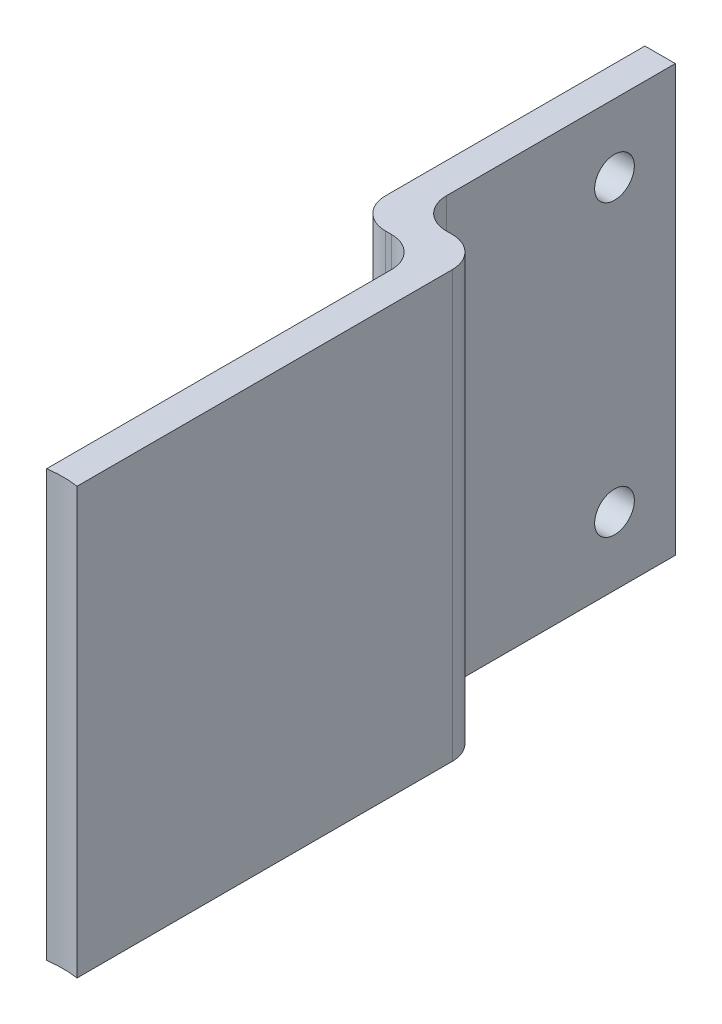
SolidWorks part; units mm, degrees
ref_plane "Front Plane" through (0, 0, 0) normal (0, 0, 1) x (1, 0, 0)
ref_plane "Top Plane" through (0, 0, 0) normal (0, 1, 0) x (1, 0, 0)
ref_plane "Right Plane" through (0, 0, 0) normal (1, 0, 0) x (0, 0, -1)
sketch "Sketch1" plane through (0, 0, 0) normal (0, 1, 0) x (1, 0, 0)
  line L2 (0, -5) -> (0, -85)
  line L3 (0, -85) -> (5, -85)
  line L4 (5, 0) -> (5, -85)
  line L5 (-5, 0) -> (-6, 0)
  line L7 (0, 5) -> (-1, 5)
  line L10 (-11, 5) -> (-11, 47.65)
  line L11 (-11, 47.65) -> (-6, 47.65)
  line L12 (-6, 10) -> (-6, 47.65)
  arc A0 (5, 0) -> (0, 5) centre (0, 0) ccw
  arc A1 (-6, 0) -> (-11, 5) centre (-6, 5) cw
  arc A2 (-5, 0) -> (0, -5) centre (-5, -5) cw
  arc A3 (-6, 10) -> (-1, 5) centre (-1, 10) ccw
  dimension "D2" = 5
  dimension "D4" = 5
  dimension "D7" = 5
  dimension "D1" = 5
  dimension "D3" = 5
  dimension "D5" = 5
  dimension "D6" = 42.65
extrude "Boss-Extrude1" add sketch "Sketch1" along normal blind 70
sketch "Sketch2" plane through (-6, 0, 0) normal (1, 0, 0) x (0, 0, -1)
  line L0 (10, 70) -> (47.65, 70) construction
  line L2 (47.65, 70) -> (47.65, 0) construction
  circle A0 centre (37.65, 58.8125) radius 3.2639
  circle A1 centre (37.65, 11.1875) radius 3.2639
  dimension "D1" = 6.5278
  dimension "D2" = 6.5278
  dimension "D3" = 47.625
  dimension "D4" = 11.1875
  dimension "D5" = 10
extrude "Cut-Extrude1" cut sketch "Sketch2" against normal blind 70
sketch "Sketch3" plane through (0, 70, 0) normal (0, 1, 0) x (1, 0, 0)
  line L0 (-6, 47.65) -> (-11, 47.65) construction
  line L1 (0, -85) -> (5, -85) construction
  circle A0 centre (2.5, -79) radius 17.5
  point P4 (0, 0)
  point P7 (2.5, -85)
  dimension "D1" = 35
  dimension "D2" = 126.65
extrude "Cut-Extrude2" cut sketch "Sketch3" against normal through all
